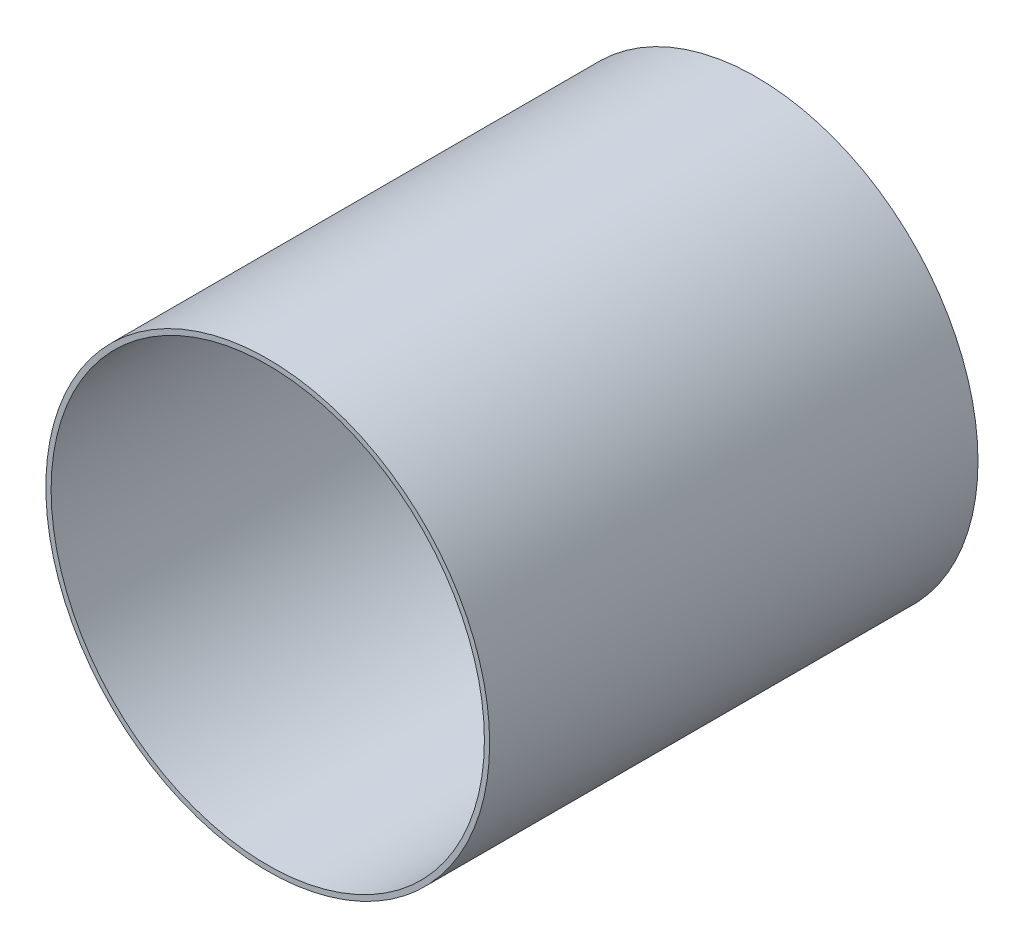
SolidWorks part; units mm, degrees
ref_plane "Front Plane" through (0, 0, 0) normal (0, 0, 1) x (1, 0, 0)
ref_plane "Top Plane" through (0, 0, 0) normal (0, 1, 0) x (1, 0, 0)
ref_plane "Right Plane" through (0, 0, 0) normal (1, 0, 0) x (0, 0, -1)
sketch "Sketch1" plane through (0, 0, 0) normal (0, 0, 1) x (1, 0, 0)
  circle A0 centre (0, 0) radius 63.4746
  circle A1 centre (0, 0) radius 61.976
  dimension "D1" = 123.952
  dimension "D2" = 126.9492
extrude "Boss-Extrude1" add sketch "Sketch1" along normal mid plane 139.7
equation "\"AIRFRAME_OD\"= 5.15in"
equation "\"AIRFRAME_ID\"= 5.00in"
equation "\"FLAT_T\"= 0.125in"
equation "\"NOSE_EXP_L\"= 27in"
equation "\"NOSE_SHOULDER_L\"= 5in"
equation "\"MAIN_L\"= 30in"
equation "\"RECO_COUP_L\"= 10in"
equation "\"RECO_SWITCH_L\"= 2in"
equation "\"DROGUE_L\"= 20in"
equation "\"ATS_FORE_COUP_L\"= 5.5in"
equation "\"ATS_AFT_COUP_L\"= 4.5in"
equation "\"LOWER_L\"= 30in"
equation "\"FIN_N\"= 4"
equation "\"CR_AFT_X\"= 0.5in"
equation "\"CR_FORE_X\"= 9.25in"
equation "\"D1@Sketch1\"=\"COUPLER_ID\""
equation "\"D2@Sketch1\"=\"COUPLER_OD\""
equation "\"D1@Boss-Extrude1\"=\"ATS_FORE_COUP_L\""
equation "\"FIN_ROOT\"= 8in"
equation "\"FIN_X\"= 0.75in"
equation "\"MOTOR_OD\"= 3.091in"
equation "\"MOTOR_ID\"= 3.00in"
equation "\"COUPLER_OD\"= 4.998in"
equation "\"COUPLER_ID\"= 4.88in"
equation "\"RECO_ROD_X\"= 3.5in"
equation "\"ATS_ROD_X\"= 3.75in"
equation "\"MOTOR_L\"= 14in"
equation "\"MOTOR_LOWER_X\"= 2in"
